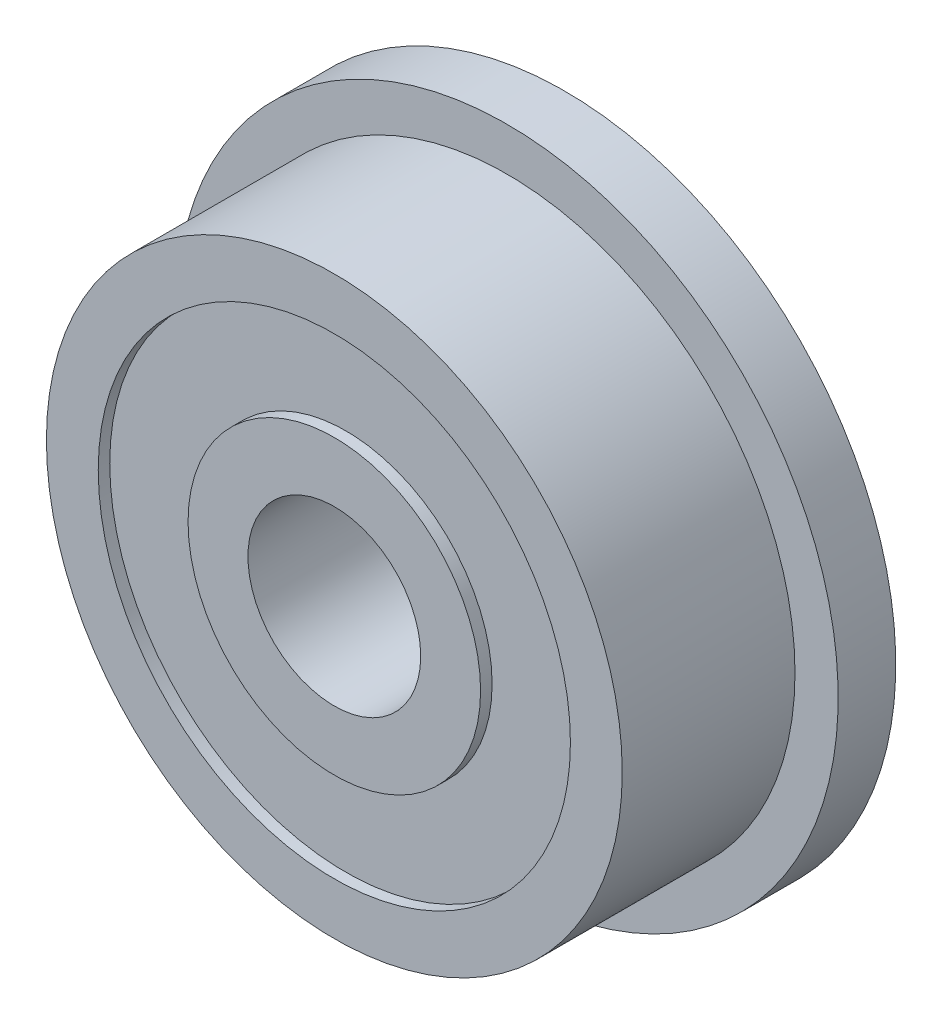
SolidWorks part; units mm, degrees
material "鉻不鏽鋼"
ref_plane "前基準面" through (0, 0, 0) normal (0, 0, 1) x (1, 0, 0)
ref_plane "上基準面" through (0, 0, 0) normal (0, 1, 0) x (1, 0, 0)
ref_plane "右基準面" through (0, 0, 0) normal (1, 0, 0) x (0, 0, -1)
sketch "草圖1" plane through (0, 0, 0) normal (0, 0, 1) x (1, 0, 0)
  circle A0 centre (0, 0) radius 5
  dimension "D1" = 10
extrude "填料-伸長1" add sketch "草圖1" along normal mid plane 4
sketch "草圖4" plane through (0, 0, -2) normal (0, 0, -1) x (-1, 0, 0)
  circle A0 centre (0, 0) radius 5.75
  dimension "D1" = 11.5
extrude "填料-伸長2" add sketch "草圖4" against normal blind 1
sketch "草圖2" plane through (0, 0, 2) normal (0, 0, 1) x (1, 0, 0)
  circle A0 centre (0, 0) radius 1.5
  dimension "D1" = 3
extrude "除料-伸長1" cut sketch "草圖2" against normal through all
sketch "草圖3" plane through (0, 0, 2) normal (0, 0, 1) x (1, 0, 0)
  circle A0 centre (0, 0) radius 2.54
  circle A1 centre (0, 0) radius 4.1
  dimension "D1" = 8.2
  dimension "D2" = 5.08
extrude "除料-伸長2" cut sketch "草圖3" against normal blind 0.2
mirror "鏡射1" about plane through (0, 0, 0) normal (0, 0, 1) of "除料-伸長2"
